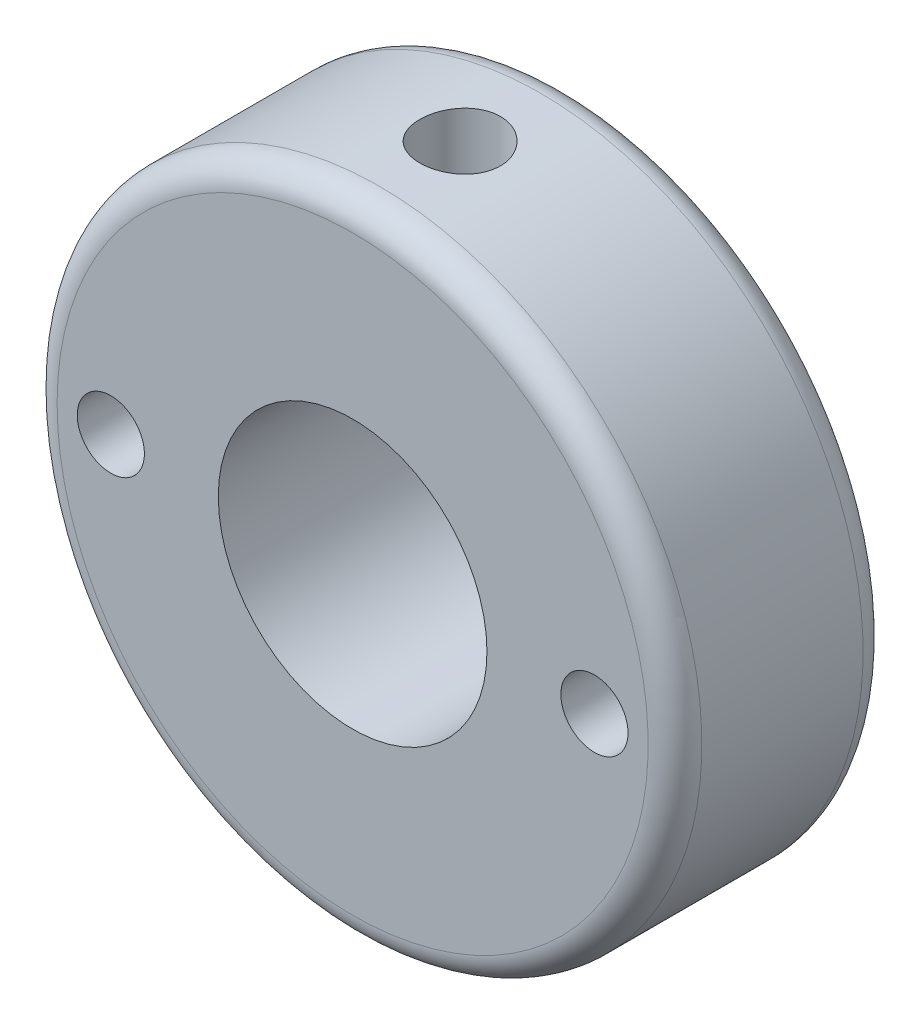
SolidWorks part; units mm, degrees
material "Malleable Cast Iron"
ref_plane "Front Plane" through (0, 0, 0) normal (0, 0, 1) x (1, 0, 0)
ref_plane "Top Plane" through (0, 0, 0) normal (0, 1, 0) x (1, 0, 0)
ref_plane "Right Plane" through (0, 0, 0) normal (1, 0, 0) x (0, 0, -1)
sketch "Sketch1" plane through (0, 0, 0) normal (0, 0, 1) x (1, 0, 0)
  line L1 (-12, -12) -> (12, -12)
  line L2 (-12, -12) -> (-12, 12)
  line L3 (-12, 12) -> (12, 12)
  line L4 (12, -12) -> (12, 12)
  line L5 (-12, -12) -> (12, 12) construction
  line L6 (-12, 12) -> (12, -12) construction
  point P0 (0, 0)
  dimension "D1" = 24
  dimension "D2" = 24
  dimension "D3" = 0
extrude "Boss-Extrude1" add sketch "Sketch1" along normal blind 8
hole_wizard "M3 Tapped Hole1" positions "Sketch6" profile "Sketch8" tap size "M3" standard "ISO" end condition through all
sketch "Sketch6" plane through (0, 0, 8) normal (0, 0, 1) x (1, 0, 0)
  point P0 (9, 0)
  point P2 (-9, 0)
  dimension "D1" = 9
  dimension "D2" = 9
cosmetic thread "Hole Thread1" parameters "D2"=3
cosmetic thread "Hole Thread2" parameters "D2"=3
sketch "Sketch8" plane through (9, 0, 8) normal (1, 0, 0) x (0, -1, 0)
  line L0 (0, 0) -> (0, 8)
  line L1 (0, 8) -> (1.25, 8)
  line L2 (1.25, 8) -> (1.25, 0)
  line L5 (1.25, 0) -> (0, 0)
  line L11 (0, -6.35) -> (0, 107.95) construction
  dimension "Thru Tap Drill Dia." = 2.5
  dimension "Thru Tap Drill Depth" = 8
hole_wizard "Ø10.0 (10) Diameter Hole1" positions "Sketch9" profile "Sketch11" hole size "Ø10.0" standard "ISO" end condition through all
sketch "Sketch9" plane through (0, 0, 0) normal (0, 0, -1) x (-1, 0, 0)
  point P0 (0, 0)
  dimension "D1" = 0
sketch "Sketch11" plane through (0, 0, 0) normal (1, 0, 0) x (0, 1, 0)
  line L0 (0, 0) -> (0, 8)
  line L1 (0, 8) -> (5, 8)
  line L2 (5, 8) -> (5, 0)
  line L5 (5, 0) -> (0, 0)
  line L11 (0, -6.35) -> (0, 107.95) construction
  dimension "Thru Hole Dia." = 10
  dimension "Thru Hole Depth" = 8
hole_wizard "Ø3.0mm Dowel Hole1" positions "Sketch12" profile "Sketch14" hole size "Ø3.0" standard "ISO"
sketch "Sketch12" plane through (0, 12, 0) normal (0, 1, 0) x (1, 0, 0)
  line L0 (12, 0) -> (-12, 0) construction
  point P0 (0, -4)
  dimension "D1" = 4
sketch "Sketch14" plane through (0, 12, 4) normal (1, 0, 0) x (0, 0, 1)
  line L0 (0, 0) -> (0, 7)
  line L1 (0, 7) -> (1.5, 7)
  line L2 (1.5, 7) -> (1.5, 0)
  line L5 (1.5, 0) -> (0, 0)
  line L11 (0, -6.35) -> (0, 107.95) construction
  dimension "Thru Hole Dia." = 3
  dimension "Thru Hole Depth" = 7
sketch "Sketch15" plane through (0, 0, 8) normal (0, 0, 1) x (1, 0, 0)
  circle A0 centre (0, 0) radius 12
  circle A1 centre (0, 0) radius 16.9706
  dimension "D1" = 24
  dimension "D2" = 24
extrude "Cut-Extrude1" cut sketch "Sketch15" against normal blind 10
fillet "Fillet1" radius 1 2 edges at (-12, 0, 0) (12, 0, 8)
